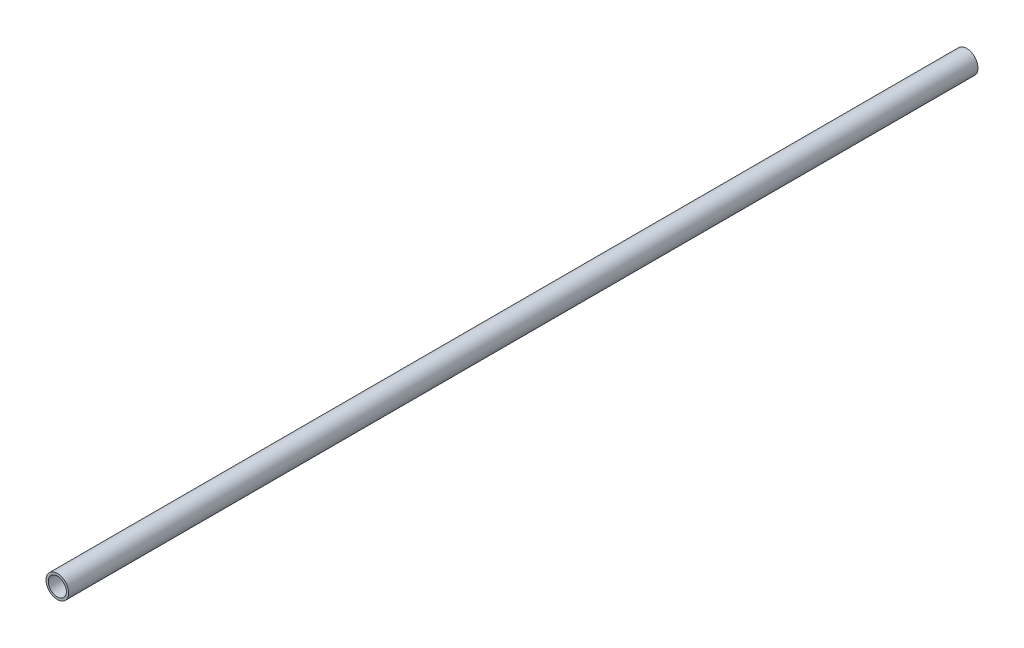
SolidWorks part; units mm, degrees
ref_plane "Front Plane" through (0, 0, 0) normal (0, 0, 1) x (1, 0, 0)
ref_plane "Top Plane" through (0, 0, 0) normal (0, 1, 0) x (1, 0, 0)
ref_plane "Right Plane" through (0, 0, 0) normal (1, 0, 0) x (0, 0, -1)
sketch "Sketch1" plane through (0, 0, 0) normal (0, 0, 1) x (1, 0, 0)
  circle A0 centre (0, 0) radius 10
  circle A1 centre (0, 0) radius 8
  dimension "D1" = 20
  dimension "D2" = 2
extrude "Boss-Extrude1" add sketch "Sketch1" along normal blind 801.8
